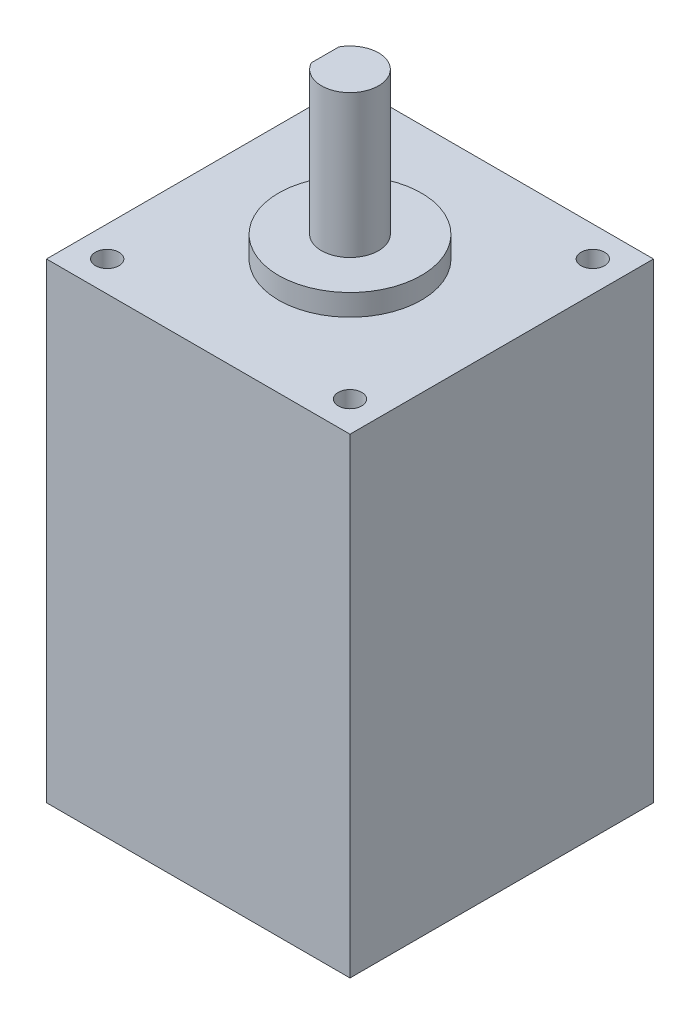
SolidWorks part; units mm, degrees
material "5052-O"
ref_plane "정면" through (0, 0, 0) normal (0, 0, 1) x (1, 0, 0)
ref_plane "윗면" through (0, 0, 0) normal (0, 1, 0) x (1, 0, 0)
ref_plane "우측면" through (0, 0, 0) normal (1, 0, 0) x (0, 0, -1)
ref_plane "평면1"
sketch "스케치1" plane through (0, 0, 0) normal (0, 1, 0) x (-1, 0, 0)
  line L0 (0, 0) -> (42.5, 0)
  line L1 (42.5, 0) -> (42.5, -42.5)
  line L2 (42.5, -42.5) -> (0, -42.5)
  line L3 (0, -42.5) -> (0, 0)
extrude "돌출1" add sketch "스케치1" along normal blind 65.95
sketch "스케치2" plane through (0, 65.95, 0) normal (0, 1, 0) x (-1, 0, 0)
  circle A0 centre (21.25, -21.25) radius 10
extrude "돌출2" add sketch "스케치2" along normal blind 3
sketch "스케치3" plane through (0, 68.95, 0) normal (0, 1, 0) x (-1, 0, 0)
  circle A0 centre (21.25, -21.25) radius 4
  dimension "D1" = 8
extrude "돌출3" add sketch "스케치3" along normal blind 20
hole_wizard "구멍3" positions "스케치5" profile "스케치4" tap size "M4" standard "ISO"
sketch "스케치5" plane through (0, 65.95, 0) normal (0, 1, 0) x (1, 0, 0)
  point P1 (-4.25, 38.25)
  point P2 (-4.25, 4.25)
  point P3 (-38.25, 4.25)
  point P4 (-38.25, 38.25)
cosmetic thread "나사산 표시1"
cosmetic thread "나사산 표시2"
sketch "스케치4" plane through (-4.25, 65.95, -38.25) normal (1, 0, 0) x (0, 0, 1)
  line L0 (0, 0) -> (0, 12.4914)
  line L1 (0, 12.4914) -> (1.65, 11.5)
  line L2 (1.65, 11.5) -> (1.65, 0)
  line L5 (1.65, 0) -> (0, 0)
  line L10 (0, 12.4914) -> (-1.65, 11.5) construction
  line L11 (0, -6.35) -> (0, 107.95) construction
  dimension "탭 드릴 지름" = 3.3
  dimension "탭 드릴 깊이" = 11.5
  dimension "드릴 각도" = 118
cosmetic thread "구멍 나사산1"
cosmetic thread "구멍 나사산3"
cosmetic thread "구멍 나사산4"
cosmetic thread "구멍 나사산5"
sketch "스케치6" plane through (0, 88.95, 0) normal (0, 1, 0) x (-1, 0, 0)
  line L0 (24.75, -19.3135) -> (24.75, -23.1865)
  arc A0 (24.75, -23.1865) -> (24.75, -19.3135) centre (21.25, -21.25) ccw
extrude "돌출4" cut sketch "스케치6" against normal blind 12
